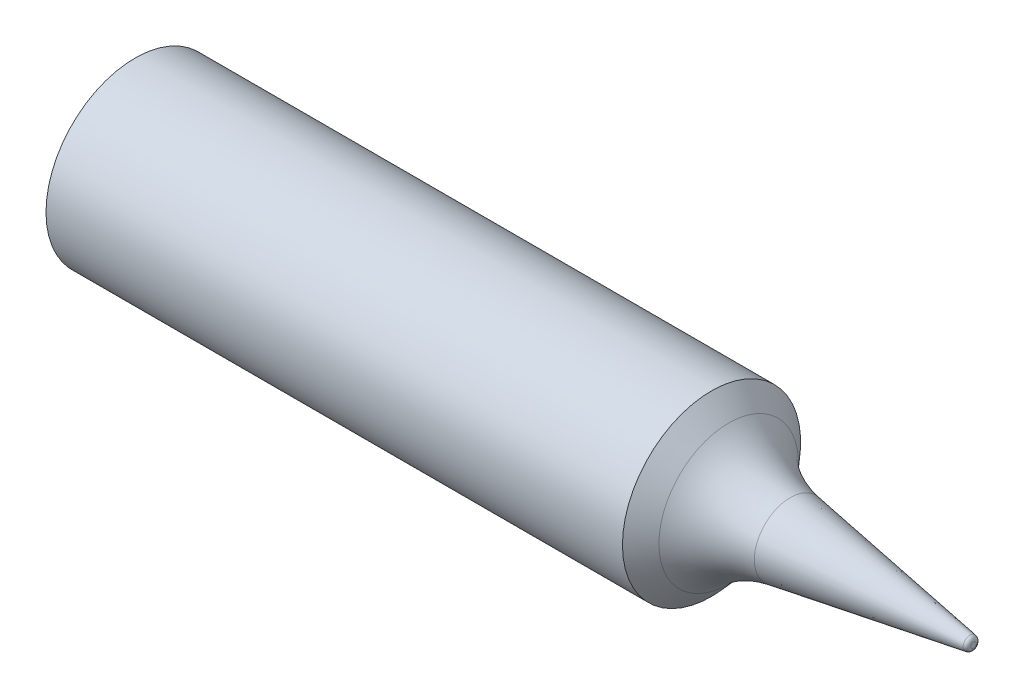
SolidWorks part; units mm, degrees
material "Acier inoxydable moulé"
ref_plane "Plan de face" through (0, 0, 0) normal (0, 0, 1) x (1, 0, 0)
ref_plane "Plan de dessus" through (0, 0, 0) normal (0, 1, 0) x (1, 0, 0)
ref_plane "Plan de droite" through (0, 0, 0) normal (1, 0, 0) x (0, 0, -1)
sketch "Esquisse1" plane through (0, 0, 0) normal (0, 0, 1) x (1, 0, 0)
  line L0 (0, 0) -> (40, 0) construction
  line L1 (0, 0) -> (0, 3.3) construction
  line L2 (0, 3.3) -> (0, 4.25)
  line L3 (0.95, 4.25) -> (27.5, 4.25)
  line L4 (40, 0) -> (40, 0.1298)
  line L5 (27.5, 4.25) -> (28.3181, 3.3296)
  line L6 (29.5, 2) -> (36, 2) construction
  line L8 (36, 2) -> (40, 2) construction
  line L9 (40, 0.3) -> (40, 2) construction
  line L10 (0, 3.3) -> (27.0734, 3.3)
  line L11 (27.0734, 3.3) -> (30.0067, 0)
  line L12 (30.0067, 0) -> (40, 0)
  line L13 (0, 4.25) -> (0, 4.95) construction
  line L14 (0, 4.95) -> (0.95, 4.95) construction
  line L15 (0.95, 4.95) -> (0.95, 4.25) construction
  line L16 (0, 4.25) -> (0.95, 4.25)
  line L17 (39.832, 0.3272) -> (31.2561, 1.7157)
  arc A0 (28.3181, 3.3296) -> (31.2561, 1.7157) centre (32.0552, 6.6514) ccw
  arc A1 (39.832, 0.3272) -> (40, 0.1298) centre (39.8, 0.1298) cw
  dimension "D11" = 5
  dimension "D12" = 0.2
  dimension "D1" = 40
  dimension "D2" = 3.3
  dimension "D3" = 4.25
  dimension "D4" = 27.5
  dimension "D5" = 2
  dimension "D6" = 2
  dimension "D7" = 0.95
  dimension "D8" = 1.7
  dimension "D9" = 0.95
  dimension "D10" = 0.7
revolve "Révolution1" add sketch "Esquisse1" angle 360 about L0
